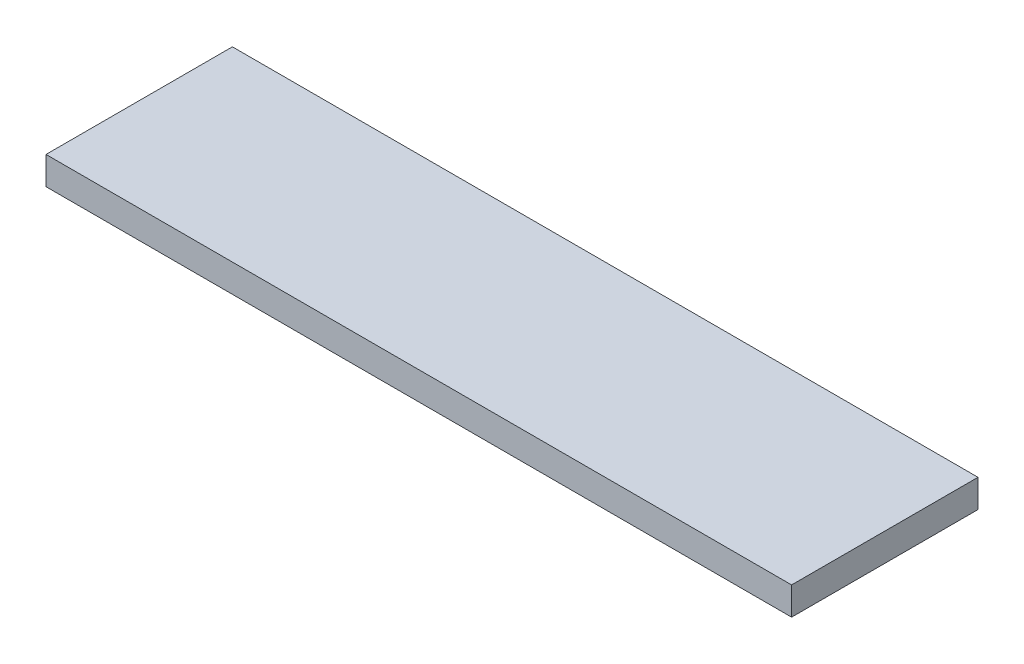
SolidWorks part; units mm, degrees
material "Balsa"
ref_plane "Plan de face" through (0, 0, 0) normal (0, 0, 1) x (1, 0, 0)
ref_plane "Plan de dessus" through (0, 0, 0) normal (0, 1, 0) x (1, 0, 0)
ref_plane "Plan de droite" through (0, 0, 0) normal (1, 0, 0) x (0, 0, -1)
sketch "Esquisse1" plane through (0, 0, 0) normal (0, 1, 0) x (1, 0, 0)
  line L1 (0, 0) -> (400, 0)
  line L2 (0, 0) -> (0, 100)
  line L3 (0, 100) -> (400, 100)
  line L4 (400, 0) -> (400, 100)
  dimension "D1" = 400
  dimension "D2" = 100
extrude "Boss.-Extru.1" add sketch "Esquisse1" along normal blind 15
